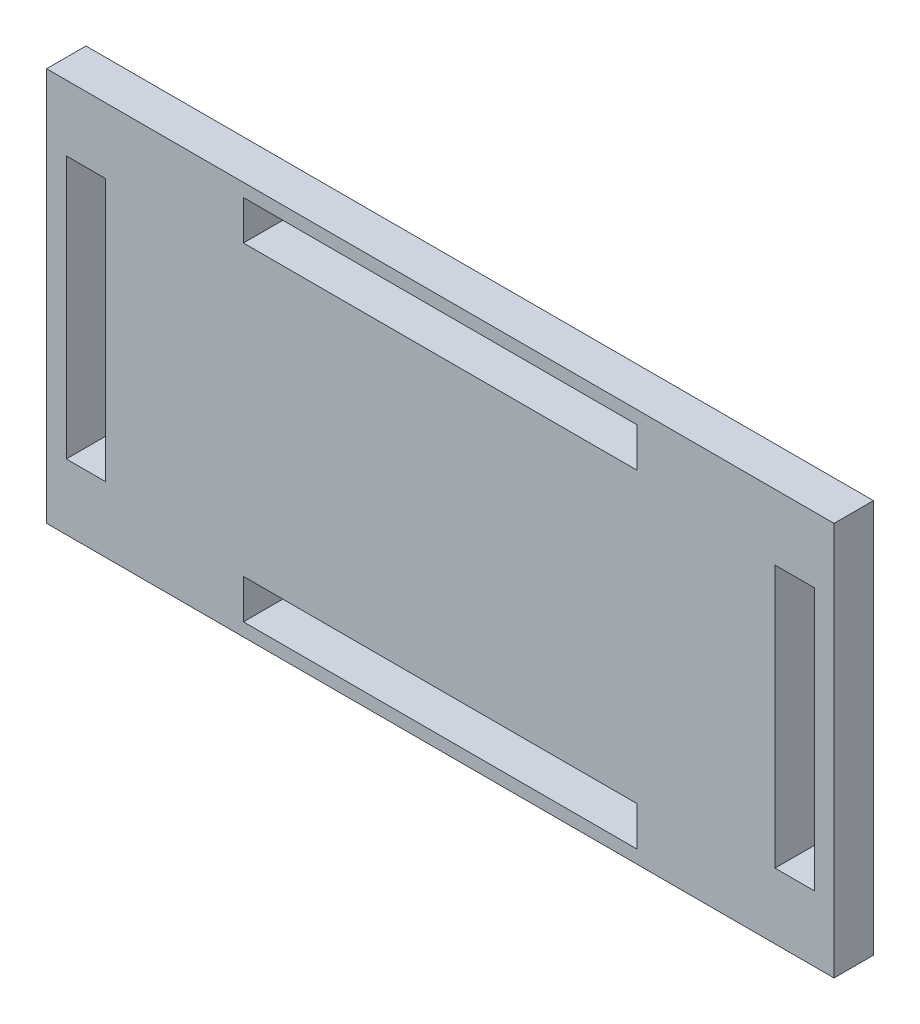
SolidWorks part; units mm, degrees
ref_plane "Front Plane" through (0, 0, 0) normal (0, 0, 1) x (1, 0, 0)
ref_plane "Top Plane" through (0, 0, 0) normal (0, 1, 0) x (1, 0, 0)
ref_plane "Right Plane" through (0, 0, 0) normal (1, 0, 0) x (0, 0, -1)
sketch "Sketch1" plane through (0, 0, 0) normal (0, 0, 1) x (1, 0, 0)
  line L1 (-30, 15) -> (30, 15)
  line L2 (-30, 15) -> (-30, -15)
  line L3 (-30, -15) -> (30, -15)
  line L4 (30, 15) -> (30, -15)
  line L5 (-30, 15) -> (30, -15) construction
  line L6 (-30, -15) -> (30, 15) construction
  line L7 (-28.5, 10) -> (-25.5, 10)
  line L8 (-28.5, 10) -> (-28.5, -10)
  line L9 (-28.5, -10) -> (-25.5, -10)
  line L10 (-25.5, 10) -> (-25.5, -10)
  line L11 (25.5, 10) -> (28.5, 10)
  line L12 (25.5, 10) -> (25.5, -10)
  line L13 (25.5, -10) -> (28.5, -10)
  line L14 (28.5, 10) -> (28.5, -10)
  line L15 (-15, 14) -> (15, 14)
  line L16 (-15, 14) -> (-15, 11)
  line L17 (-15, 11) -> (15, 11)
  line L18 (15, 14) -> (15, 11)
  line L19 (-15, -11) -> (15, -11)
  line L20 (-15, -11) -> (-15, -14)
  line L21 (-15, -14) -> (15, -14)
  line L22 (15, -11) -> (15, -14)
  point P0 (0, 0)
  dimension "D1" = 60
  dimension "D2" = 30
  dimension "D3" = 1.5
  dimension "D4" = 4.5
  dimension "D5" = 1.5
  dimension "D6" = 4.5
  dimension "D7" = 5
  dimension "D8" = 5
  dimension "D9" = 5
  dimension "D10" = 5
  dimension "D11" = 1
  dimension "D12" = 15
  dimension "D13" = 30
  dimension "D14" = 3
  dimension "D15" = 3
  dimension "D16" = 1
  dimension "D17" = 15
  dimension "D18" = 30
extrude "Boss-Extrude1" add sketch "Sketch1" along normal mid plane 3
